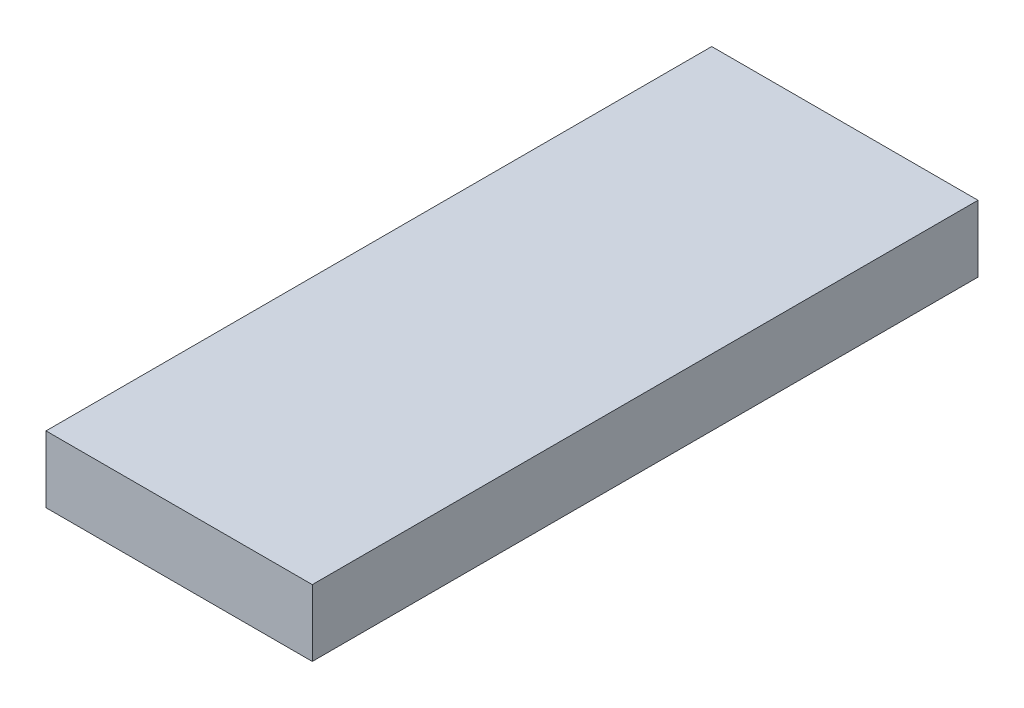
SolidWorks part; units mm, degrees
ref_plane "Front Plane" through (0, 0, 0) normal (0, 0, 1) x (1, 0, 0)
ref_plane "Top Plane" through (0, 0, 0) normal (0, 1, 0) x (1, 0, 0)
ref_plane "Right Plane" through (0, 0, 0) normal (1, 0, 0) x (0, 0, -1)
sketch "Sketch1" plane through (0, 0, 0) normal (0, 1, 0) x (1, 0, 0)
  line L0 (-20, 50) -> (20, -50) construction
  line L1 (-20, 50) -> (20, 50)
  line L2 (-20, 50) -> (-20, -50)
  line L3 (-20, -50) -> (20, -50)
  line L4 (20, 50) -> (20, -50)
  dimension "D1" = 40
  dimension "D2" = 100
extrude "Boss-Extrude1" add sketch "Sketch1" along normal blind 10
